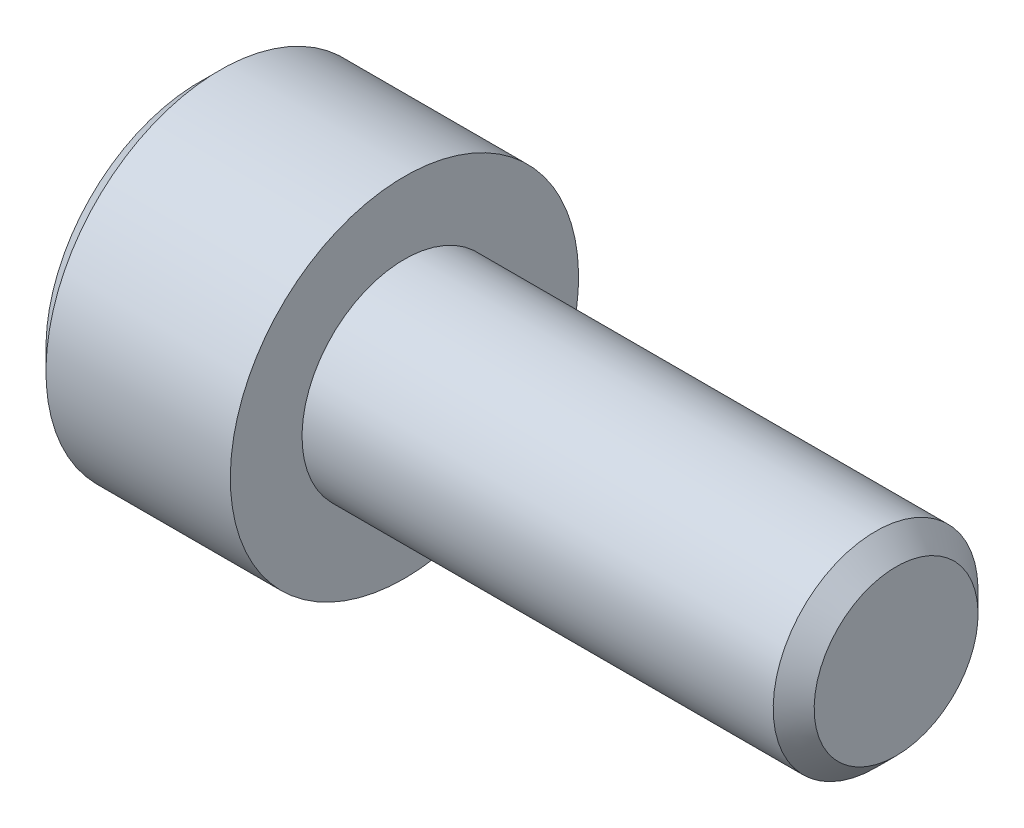
SolidWorks part; units mm, degrees
ref_plane "Front" through (0, 0, 0) normal (0, 0, 1) x (1, 0, 0)
ref_plane "Top" through (0, 0, 0) normal (0, 1, 0) x (1, 0, 0)
ref_plane "Right" through (0, 0, 0) normal (1, 0, 0) x (0, 0, -1)
ref_plane "Plane1" through (0, 0, 0) normal (0, 0, 1) x (1, 0, 0)
sketch "Sketch1" plane through (0, 0, 0) normal (0, 0, 1) x (1, 0, 0)
  line L0 (-5, 0) -> (-5, 3.75)
  line L1 (-5, 3.75) -> (-4.5, 4.25)
  line L2 (-4.5, 4.25) -> (0, 4.25)
  line L3 (0, 4.25) -> (0, 2.5)
  line L4 (0, 2.5) -> (12, 2.5)
  line L6 (12, 2.5) -> (12, 0)
  line L7 (12, 0) -> (-5, 0)
  line L8 (12, 0) -> (-5, 0) construction
  dimension "D1" = 2.5
  dimension "D2" = 12
  dimension "D3" = 5
  dimension "D4" = 4.25
revolve "Revolve1" add sketch "Sketch1" angle 360 about L8
ref_plane "Plane2" through (0, 0, 0) normal (0, 0, 1) x (1, 0, 0)
chamfer "Chamfer1" distance 0.5 angle 45 1 edges at (12, -2.5, 0)
sketch "Sketch2" plane through (0, 0, 0) normal (0, 0, 1) x (1, 0, 0)
  line L0 (-5, 0) -> (-5, 2)
  line L1 (-5, 2) -> (-2.5, 2)
  line L2 (-2.5, 2) -> (-1.9641, 0)
  line L3 (-1.9641, 0) -> (-5, 0)
  line L4 (-1.9641, 0) -> (-5, 0) construction
revolve "Cut-Revolve1" cut sketch "Sketch2" angle 360 about L4
ref_plane "Plane3" through (-5, 0, 0) normal (1, 0, 0) x (0, 0, -1)
sketch "Sketch3" plane through (-5, 0, 0) normal (1, 0, 0) x (0, 0, -1)
  line L0 (-2, 1.1547) -> (-2, -1.1547)
  line L1 (-2, -1.1547) -> (0, -2.3094)
  line L2 (0, -2.3094) -> (2, -1.1547)
  line L3 (2, -1.1547) -> (2, 1.1547)
  line L4 (2, 1.1547) -> (0, 2.3094)
  line L5 (0, 2.3094) -> (-2, 1.1547)
extrude "Cut-Extrude1" cut sketch "Sketch3" along normal blind 2.5
